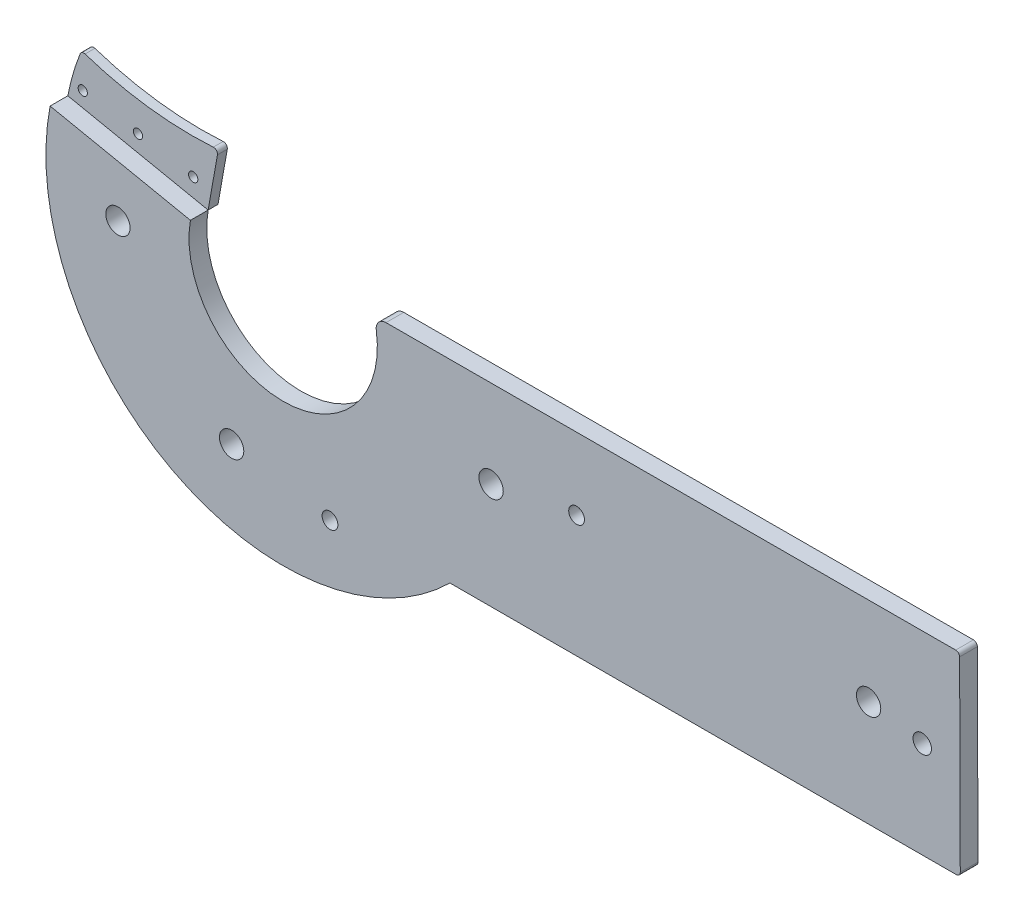
SolidWorks part; units mm, degrees
ref_plane "Plano frontal" through (0, 0, 0) normal (0, 0, 1) x (1, 0, 0)
ref_plane "Plano superior" through (0, 0, 0) normal (0, 1, 0) x (1, 0, 0)
ref_plane "Plano direito" through (0, 0, 0) normal (1, 0, 0) x (0, 0, -1)
sketch "Esboço1" plane through (0, 0, 0) normal (0, 0, 1) x (1, 0, 0)
  line L0 (428.3038, 137.7921) -> (428.5303, 38.9923) construction
  line L1 (131.185, 136.9413) -> (428.4919, 137.5934)
  line L2 (428.4919, 137.5934) -> (428.8313, 39.0387)
  line L3 (169.7841, 38.7089) -> (428.8313, 39.0387)
  line L4 (38.0785, 132.2887) -> (-33.1431, 146.9082)
  arc A0 (38.0785, 132.2887) -> (131.185, 136.9413) centre (85.1607, 124.0299) ccw
  arc A1 (-33.1431, 146.9082) -> (169.7841, 38.7089) centre (85.1478, 124.3681) ccw
  circle A2 centre (190.695, 92.6157) radius 6.175
  circle A3 centre (382.2974, 92.724) radius 6.175
  circle A4 centre (409.5211, 88.0049) radius 4.675
  circle A5 centre (234.0831, 100.6469) radius 4
  circle A6 centre (58.9921, 44.328) radius 6.175
  circle A7 centre (108.9207, 35.8266) radius 4
  circle A8 centre (1.288, 113.6268) radius 6.175
  point P3 (190.695, 92.6157)
  point P4 (70.7664, 78.4476)
  point P5 (121.0992, 92.5122)
  point P6 (392.6154, 38.9926)
  point P7 (38.1701, 115.2649)
  point P8 (404.2389, 137.5402)
  point P11 (164.845, 137.0151)
  point P12 (428.5294, 126.709)
  point P13 (234.0831, 100.6469)
  point P14 (428.7932, 50.0971)
  point P16 (190.3579, 38.7351)
  point P17 (146.8169, 20.9382)
  point P19 (382.2974, 92.724)
  point P20 (33.3928, 15.638)
  point P21 (0.5292, 38.6914)
  point P23 (409.5211, 88.0049)
  point P24 (13.8078, 137.2706)
  point P25 (34.2456, 133.0754)
  point P37 (58.9921, 44.328)
  point P40 (108.9207, 35.8266)
  point P43 (1.288, 113.6268)
  dimension "D2" = 12.35
  dimension "D3" = 9.35
  dimension "D4" = 8
  dimension "D1" = 98.8
extrude "Ressalto-extrusão1" add sketch "Esboço1" along normal blind 9
cosmetic thread "Representação de rosca1" parameters "D2"=9.525
cosmetic thread "Representação de rosca2" parameters "D2"=9.525
cosmetic thread "Representação de rosca3" parameters "D2"=9.525
sketch "Esboço2" plane through (0, 0, 0) normal (0, 0, 1) x (1, 0, 0)
  line L0 (428.3038, 137.7921) -> (428.5303, 38.9923) construction
  line L1 (131.185, 136.9413) -> (428.4919, 137.5934)
  line L2 (428.4919, 137.5934) -> (428.8313, 39.0387)
  line L3 (169.7841, 38.7089) -> (428.8313, 39.0387)
  line L4 (38.0785, 132.2887) -> (-33.1431, 146.9082)
  arc A0 (38.0785, 132.2887) -> (131.185, 136.9413) centre (85.1607, 124.0299) ccw
  arc A1 (-33.1431, 146.9082) -> (169.7841, 38.7089) centre (85.1478, 124.3681) ccw
  circle A2 centre (190.695, 92.6157) radius 6.175
  circle A3 centre (382.2974, 92.724) radius 6.175
  circle A4 centre (409.5211, 88.0049) radius 4.675
  circle A5 centre (234.0831, 100.6469) radius 4
  circle A6 centre (58.9921, 44.328) radius 6.175
  circle A7 centre (108.9207, 35.8266) radius 4
  circle A8 centre (1.288, 113.6268) radius 6.175
  point P3 (190.695, 92.6157)
  point P4 (70.7664, 78.4476)
  point P5 (121.0992, 92.5122)
  point P6 (392.6154, 38.9926)
  point P7 (38.1701, 115.2649)
  point P8 (404.2389, 137.5402)
  point P11 (164.845, 137.0151)
  point P12 (428.5294, 126.709)
  point P13 (234.0831, 100.6469)
  point P14 (428.7932, 50.0971)
  point P16 (190.3579, 38.7351)
  point P17 (146.8169, 20.9382)
  point P19 (382.2974, 92.724)
  point P20 (33.3928, 15.638)
  point P21 (0.5292, 38.6914)
  point P23 (409.5211, 88.0049)
  point P24 (13.8078, 137.2706)
  point P25 (34.2456, 133.0754)
  point P37 (58.9921, 44.328)
  point P40 (108.9207, 35.8266)
  point P43 (1.288, 113.6268)
  dimension "D2" = 12.35
  dimension "D3" = 9.35
  dimension "D4" = 8
  dimension "D1" = 98.8
sketch "Esboço3" plane through (0, 0, 0) normal (0, 0, -1) x (-1, 0, 0)
  line L0 (-43.2397, 161.4284) -> (-38.0785, 132.2887)
  line L2 (33.1431, 146.9082) -> (-38.0785, 132.2887)
  line L3 (-38.0785, 132.2887) -> (33.1431, 146.9082) construction
  line L4 (-2.4677, 139.5984) -> (-2.4677, 172.3313) construction
  line L5 (-30.4851, 143.0615) -> (-2.4677, 148.0358) construction
  line L6 (23.2358, 152.5994) -> (25.5496, 153.0102) construction
  line L7 (-2.4677, 148.0358) -> (25.5496, 153.0102) construction
  arc A0 (33.1431, 146.9082) -> (26.186, 170.2546) centre (-85.1478, 124.3681) ccw
  arc A1 (-169.7841, 38.7089) -> (33.1431, 146.9082) centre (-85.1478, 124.3681) ccw construction
  arc A2 (-43.2397, 161.4284) -> (26.186, 170.2546) centre (-29.808, 333.2362) ccw
  circle A3 centre (-2.4677, 148.0358) radius 2.35
  circle A4 centre (-30.4851, 143.0615) radius 2.35
  circle A5 centre (25.5496, 153.0102) radius 2.35
  point P0 (-38.6398, 135.4575)
  point P1 (-40.8676, 148.0358)
  point P3 (-16.4883, 161.4197)
  point P9 (-40.8676, 161.2595)
  point P14 (-4.5845, 162.7601)
  point P17 (-2.4677, 148.0358)
  point P18 (-30.4851, 143.0615)
  dimension "D1" = 4.7
extrude "Ressalto-extrusão2" add sketch "Esboço3" along normal blind 5 separate body
cosmetic thread "Representação de rosca4" parameters "D2"=6.35
cosmetic thread "Representação de rosca5" parameters "D2"=6.35
cosmetic thread "Representação de rosca6" parameters "D2"=6.35
fillet "Filete1" radius 2 2 edges at (-26.186, 170.2546, -2.5) (43.2397, 161.4284, -2.5)
fillet "Filete2" radius 5 1 edges at (131.185, 136.9413, 4.5)
fillet "Filete3" radius 2 2 edges at (428.4919, 137.5934, 4.5) (428.8313, 39.0387, 4.5)
